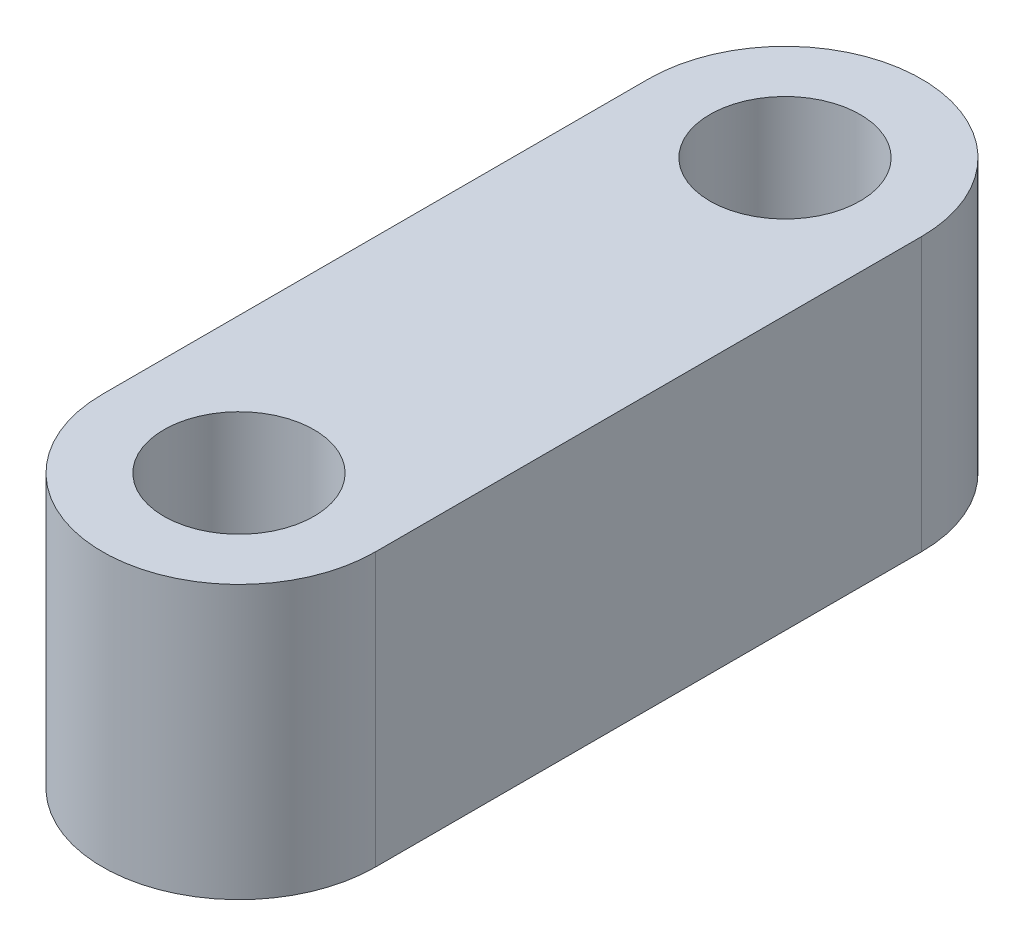
SolidWorks part; units mm, degrees
ref_plane "Front Plane" through (0, 0, 0) normal (0, 0, 1) x (1, 0, 0)
ref_plane "Top Plane" through (0, 0, 0) normal (0, 1, 0) x (1, 0, 0)
ref_plane "Right Plane" through (0, 0, 0) normal (1, 0, 0) x (0, 0, -1)
sketch "Sketch3" plane through (0, 0, 0) normal (0, 1, 0) x (1, 0, 0)
  line L0 (0, 0) -> (0, 20)
  line L1 (5, 20) -> (5, 0)
  line L2 (-5, 20) -> (-5, 0)
  circle A0 centre (0, 20) radius 5
  circle A1 centre (0, 0) radius 5
  circle A2 centre (0, 20) radius 2.75
  circle A3 centre (0, 0) radius 2.75
extrude "Boss-Extrude1" add sketch "Sketch3" along normal blind 10
